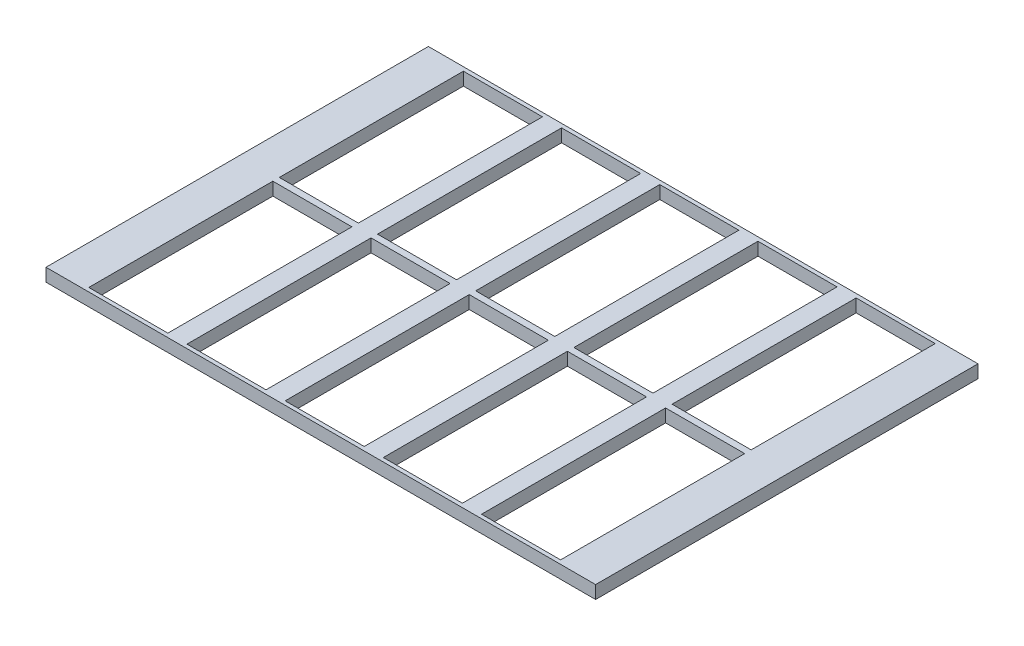
SolidWorks part; units mm, degrees
ref_plane "Front Plane" through (0, 0, 0) normal (0, 0, 1) x (1, 0, 0)
ref_plane "Top Plane" through (0, 0, 0) normal (0, 1, 0) x (1, 0, 0)
ref_plane "Right Plane" through (0, 0, 0) normal (1, 0, 0) x (0, 0, -1)
sketch "Sketch1" plane through (0, 0, 0) normal (0, 1, 0) x (1, 0, 0)
  line L1 (-212, 147.5) -> (212, 147.5)
  line L2 (-212, 147.5) -> (-212, -147.5)
  line L3 (-212, -147.5) -> (212, -147.5)
  line L4 (212, 147.5) -> (212, -147.5)
  line L5 (-212, 147.5) -> (212, -147.5) construction
  line L6 (-212, -147.5) -> (212, 147.5) construction
  line L7 (-182, 144.5) -> (-121, 144.5)
  line L8 (-182, 144.5) -> (-182, 2.5)
  line L9 (-182, 2.5) -> (-121, 2.5)
  line L45 (-121, 2.5) -> (-121, 144.5)
  line L47 (-45.25, 2.5) -> (-45.25, 144.5)
  line L48 (-106.25, 144.5) -> (-45.25, 144.5)
  line L49 (-106.25, 144.5) -> (-106.25, 2.5)
  line L50 (-106.25, 2.5) -> (-45.25, 2.5)
  line L51 (30.5, 2.5) -> (30.5, 144.5)
  line L52 (-30.5, 144.5) -> (30.5, 144.5)
  line L53 (-30.5, 144.5) -> (-30.5, 2.5)
  line L54 (-30.5, 2.5) -> (30.5, 2.5)
  line L55 (106.25, 2.5) -> (106.25, 144.5)
  line L56 (45.25, 144.5) -> (106.25, 144.5)
  line L57 (45.25, 144.5) -> (45.25, 2.5)
  line L58 (45.25, 2.5) -> (106.25, 2.5)
  line L59 (182, 2.5) -> (182, 144.5)
  line L60 (121, 144.5) -> (182, 144.5)
  line L61 (121, 144.5) -> (121, 2.5)
  line L62 (121, 2.5) -> (182, 2.5)
  line L63 (-267.8843, 0) -> (244.8437, 0) construction
  line L65 (121, -2.5) -> (182, -2.5)
  line L66 (121, -144.5) -> (121, -2.5)
  line L67 (121, -144.5) -> (182, -144.5)
  line L68 (182, -2.5) -> (182, -144.5)
  line L69 (45.25, -2.5) -> (106.25, -2.5)
  line L70 (45.25, -144.5) -> (45.25, -2.5)
  line L71 (45.25, -144.5) -> (106.25, -144.5)
  line L72 (106.25, -2.5) -> (106.25, -144.5)
  line L73 (-30.5, -2.5) -> (30.5, -2.5)
  line L74 (-30.5, -144.5) -> (-30.5, -2.5)
  line L75 (-30.5, -144.5) -> (30.5, -144.5)
  line L76 (30.5, -2.5) -> (30.5, -144.5)
  line L77 (-106.25, -2.5) -> (-45.25, -2.5)
  line L78 (-106.25, -144.5) -> (-106.25, -2.5)
  line L79 (-106.25, -144.5) -> (-45.25, -144.5)
  line L80 (-45.25, -2.5) -> (-45.25, -144.5)
  line L81 (-182, -2.5) -> (-121, -2.5)
  line L82 (-182, -144.5) -> (-182, -2.5)
  line L83 (-182, -144.5) -> (-121, -144.5)
  line L84 (-121, -2.5) -> (-121, -144.5)
  point P0 (0, 0)
  dimension "D8" = 30
  dimension "D1" = 424
  dimension "D2" = 295
  dimension "D3" = 142
  dimension "D4" = 3
  dimension "D5" = 61
  dimension "D6" = 30
  dimension "D9" = 3
  dimension "D7" = 5
extrude "Boss-Extrude1" add sketch "Sketch1" along normal blind 10
